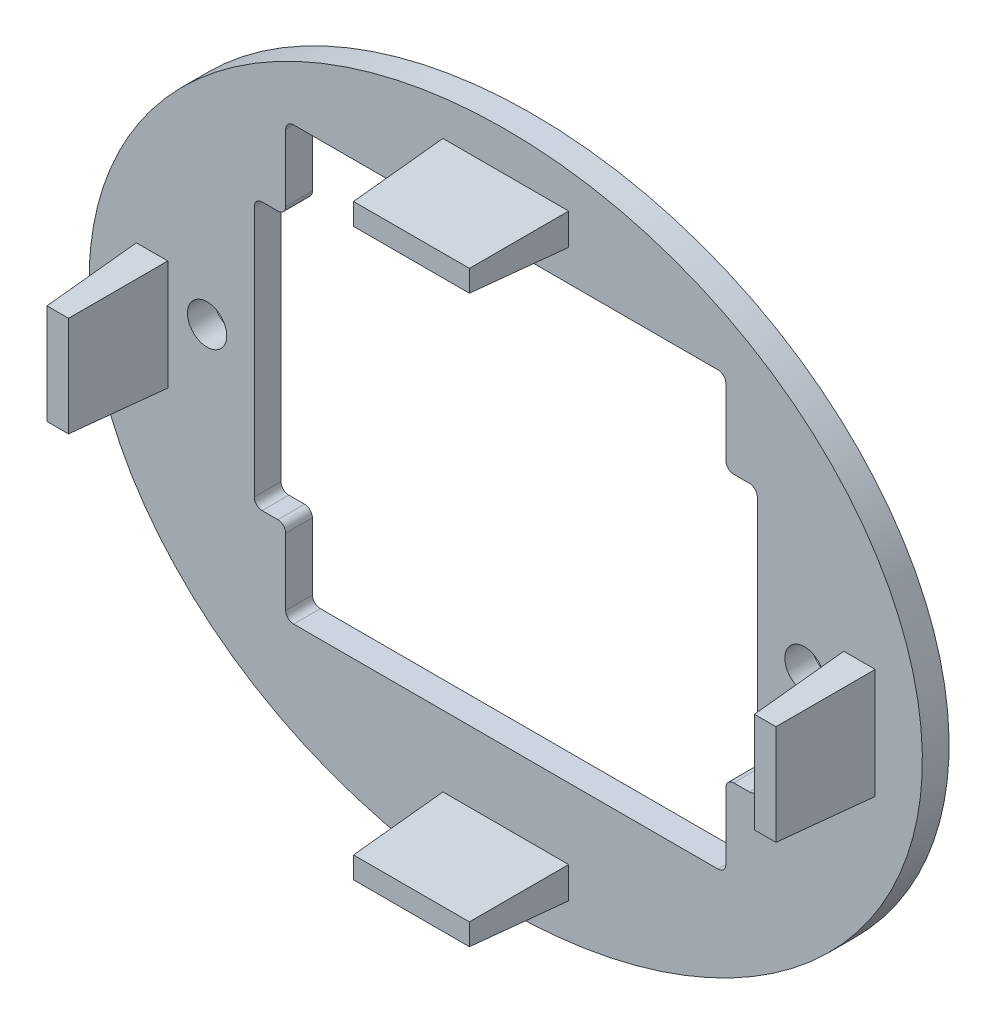
SolidWorks part; units mm, degrees
ref_plane "Front Plane" through (0, 0, 0) normal (0, 0, 1) x (1, 0, 0)
ref_plane "Top Plane" through (0, 0, 0) normal (0, 1, 0) x (1, 0, 0)
ref_plane "Right Plane" through (0, 0, 0) normal (1, 0, 0) x (0, 0, -1)
sketch "Sketch1" plane through (0, 0, 0) normal (0, 0, 1) x (1, 0, 0)
  line L0 (0, 0) -> (0, 27.1717) construction
  line L1 (-14, 15) -> (14, 15)
  line L2 (-14, 15) -> (-14, 9.75)
  line L3 (-14, -12.5) -> (14, -12.5)
  line L4 (14, 15) -> (14, 9.75)
  line L5 (-14, 9.75) -> (-16, 9.75)
  line L7 (-14, -7.25) -> (-16, -7.25)
  line L8 (-16, 9.75) -> (-16, -7.25)
  line L9 (14, -7.25) -> (16, -7.25)
  line L10 (16, 9.75) -> (16, -7.25)
  line L11 (14, 9.75) -> (16, 9.75)
  line L13 (-14, -7.25) -> (-14, -12.5)
  line L14 (14, -7.25) -> (14, -12.5)
  circle A0 centre (-19, 1.25) radius 1.25
  circle A1 centre (19, 1.25) radius 1.25
  ellipse E0 centre (0, 0) end of major axis (-26.5, 0) minor radius 21.5
  point P18 (-15, 9.75)
  point P25 (-41.8478, 14.0658)
  dimension "D12" = 2.5
  dimension "D1" = 43
  dimension "D2" = 53
  dimension "D3" = 14
  dimension "D5" = 6.5
  dimension "D6" = 27.5
  dimension "D7" = 13.75
  dimension "D8" = 2
  dimension "D9" = 5.25
  dimension "D10" = 5.25
  dimension "D11" = 5
extrude "Boss-Extrude1" add sketch "Sketch1" along normal blind 1.7
fillet "Fillet1" radius 0.5 12 edges at (16, 9.75, 0.85) (14, 9.75, 0.85) (14, 15, 0.85) (14, -12.5, 0.85) (16, -7.25, 0.85) (14, -7.25, 0.85) (-14, -12.5, 0.85) (-14, -7.25, 0.85) (-16, -7.25, 0.85) (-14, 15, 0.85) (-14, 9.75, 0.85) (-16, 9.75, 0.85)
sketch "Sketch2" plane through (0, 0, 1.7) normal (0, 0, 1) x (1, 0, 0)
  line L0 (0, 0) -> (5.606, 0) construction
  line L1 (-23.5, 3.5) -> (-21.5, 3.5)
  line L2 (-23.5, 3.5) -> (-23.5, -3.5)
  line L3 (-23.5, -3.5) -> (-21.5, -3.5)
  line L4 (-21.5, 3.5) -> (-21.5, -3.5)
  line L5 (-4, 19) -> (4, 19)
  line L6 (-4, 19) -> (-4, 17)
  line L7 (-4, 17) -> (4, 17)
  line L8 (4, 19) -> (4, 17)
  line L9 (0, 0) -> (0, 6.9875) construction
  line L10 (-4, -17) -> (4, -17)
  line L11 (4, -19) -> (4, -17)
  line L12 (-4, -19) -> (4, -19)
  line L13 (-4, -19) -> (-4, -17)
  line L14 (23.5, -3.5) -> (21.5, -3.5)
  line L15 (21.5, 3.5) -> (21.5, -3.5)
  line L16 (23.5, 3.5) -> (21.5, 3.5)
  line L17 (23.5, 3.5) -> (23.5, -3.5)
  dimension "D1" = 7
  dimension "D2" = 3.5
  dimension "D3" = 2
  dimension "D4" = 21.5
  dimension "D5" = 2
  dimension "D6" = 8
  dimension "D7" = 4
  dimension "D8" = 17
extrude "Boss-Extrude2" add sketch "Sketch2" along normal blind 6 draft 3
